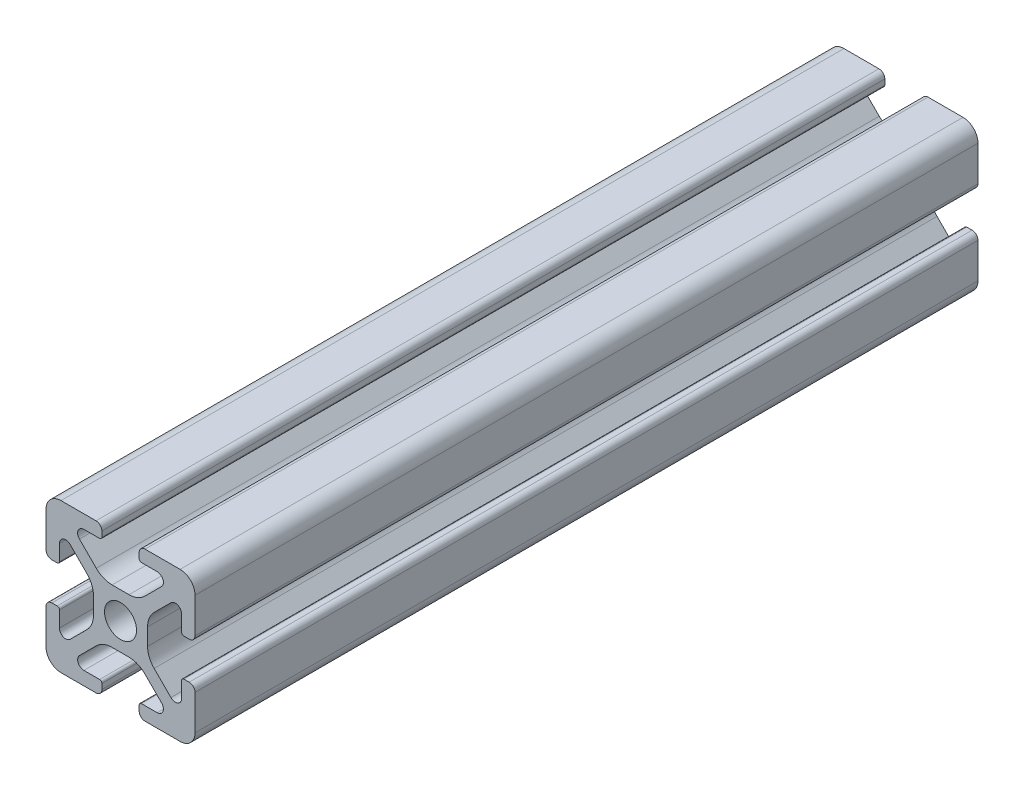
SolidWorks part; units mm, degrees
material "6061-T6 (SS)"
ref_plane "Front Plane" through (0, 0, 0) normal (0, 0, 1) x (1, 0, 0)
ref_plane "Top Plane" through (0, 0, 0) normal (0, 1, 0) x (1, 0, 0)
ref_plane "Right Plane" through (0, 0, 0) normal (1, 0, 0) x (0, 0, -1)
sketch "Sketch1" plane through (0, 0, 0) normal (0, 0, 1) x (1, 0, 0)
  line L2 (-9.9949, 7.9883) -> (-9.9949, 3.2893)
  line L3 (-7.9883, 9.9949) -> (-3.2893, 9.9949)
  line L4 (-2.5019, 9.2075) -> (-2.5019, 8.4963)
  line L5 (-2.8067, 8.1915) -> (-4.9149, 8.1915)
  line L6 (-5.5076, 6.7606) -> (-3.2528, 4.5058)
  line L7 (-6.7606, 5.5076) -> (-4.5058, 3.2528)
  line L8 (-8.1915, 4.9149) -> (-8.1915, 2.8067)
  line L9 (-8.4963, 2.5019) -> (-9.2075, 2.5019)
  line L11 (-1.1334, 3.6279) -> (1.1334, 3.6279)
  line L12 (-3.6279, 1.1334) -> (-3.6279, -1.1334)
  line L13 (8.4963, 2.5019) -> (9.2075, 2.5019)
  line L14 (8.1915, 4.9149) -> (8.1915, 2.8067)
  line L15 (9.9949, 7.9883) -> (9.9949, 3.2893)
  line L16 (7.9883, 9.9949) -> (3.2893, 9.9949)
  line L17 (2.5019, 9.2075) -> (2.5019, 8.4963)
  line L18 (2.8067, 8.1915) -> (4.9149, 8.1915)
  line L19 (3.6279, 1.1334) -> (3.6279, -1.1334)
  line L20 (5.5076, 6.7606) -> (3.2528, 4.5058)
  line L21 (6.7606, 5.5076) -> (4.5058, 3.2528)
  line L22 (-8.4963, -2.5019) -> (-9.2075, -2.5019)
  line L23 (-8.1915, -4.9149) -> (-8.1915, -2.8067)
  line L24 (-6.7606, -5.5076) -> (-4.5058, -3.2528)
  line L25 (-5.5076, -6.7606) -> (-3.2528, -4.5058)
  line L26 (-2.8067, -8.1915) -> (-4.9149, -8.1915)
  line L27 (-2.5019, -9.2075) -> (-2.5019, -8.4963)
  line L28 (-7.9883, -9.9949) -> (-3.2893, -9.9949)
  line L29 (-9.9949, -7.9883) -> (-9.9949, -3.2893)
  line L30 (9.9949, -7.9883) -> (9.9949, -3.2893)
  line L31 (7.9883, -9.9949) -> (3.2893, -9.9949)
  line L32 (2.5019, -9.2075) -> (2.5019, -8.4963)
  line L33 (2.8067, -8.1915) -> (4.9149, -8.1915)
  line L34 (5.5076, -6.7606) -> (3.2528, -4.5058)
  line L35 (6.7606, -5.5076) -> (4.5058, -3.2528)
  line L36 (8.1915, -4.9149) -> (8.1915, -2.8067)
  line L37 (8.4963, -2.5019) -> (9.2075, -2.5019)
  line L38 (-1.1334, -3.6279) -> (1.1334, -3.6279)
  circle A0 centre (0, 0) radius 2.1463
  arc A1 (-9.9949, 7.9883) -> (-7.9883, 9.9949) centre (-7.9883, 7.9883) cw
  arc A2 (-6.7606, 5.5076) -> (-8.1915, 4.9149) centre (-7.3533, 4.9149) ccw
  arc A3 (-4.9149, 8.1915) -> (-5.5076, 6.7606) centre (-4.9149, 7.3533) ccw
  arc A4 (-3.2893, 9.9949) -> (-2.5019, 9.2075) centre (-3.2893, 9.2075) cw
  arc A5 (-9.9949, 3.2893) -> (-9.2075, 2.5019) centre (-9.2075, 3.2893) ccw
  arc A6 (-8.1915, 2.8067) -> (-8.4963, 2.5019) centre (-8.4963, 2.8067) cw
  arc A7 (-2.5019, 8.4963) -> (-2.8067, 8.1915) centre (-2.8067, 8.4963) cw
  arc A8 (-1.1334, 3.6279) -> (-3.2528, 4.5058) centre (-1.1334, 6.6251) cw
  arc A9 (-3.6279, 1.1334) -> (-4.5058, 3.2528) centre (-6.6251, 1.1334) ccw
  arc A10 (8.1915, 2.8067) -> (8.4963, 2.5019) centre (8.4963, 2.8067) ccw
  arc A11 (9.9949, 3.2893) -> (9.2075, 2.5019) centre (9.2075, 3.2893) cw
  arc A12 (9.9949, 7.9883) -> (7.9883, 9.9949) centre (7.9883, 7.9883) ccw
  arc A13 (3.2893, 9.9949) -> (2.5019, 9.2075) centre (3.2893, 9.2075) ccw
  arc A14 (2.5019, 8.4963) -> (2.8067, 8.1915) centre (2.8067, 8.4963) ccw
  arc A15 (1.1334, 3.6279) -> (3.2528, 4.5058) centre (1.1334, 6.6251) ccw
  arc A16 (3.6279, 1.1334) -> (4.5058, 3.2528) centre (6.6251, 1.1334) cw
  arc A17 (6.7606, 5.5076) -> (8.1915, 4.9149) centre (7.3533, 4.9149) cw
  arc A18 (4.9149, 8.1915) -> (5.5076, 6.7606) centre (4.9149, 7.3533) cw
  arc A19 (-3.6279, -1.1334) -> (-4.5058, -3.2528) centre (-6.6251, -1.1334) cw
  arc A20 (-1.1334, -3.6279) -> (-3.2528, -4.5058) centre (-1.1334, -6.6251) ccw
  arc A21 (-2.5019, -8.4963) -> (-2.8067, -8.1915) centre (-2.8067, -8.4963) ccw
  arc A22 (-8.1915, -2.8067) -> (-8.4963, -2.5019) centre (-8.4963, -2.8067) ccw
  arc A23 (-9.9949, -3.2893) -> (-9.2075, -2.5019) centre (-9.2075, -3.2893) cw
  arc A24 (-3.2893, -9.9949) -> (-2.5019, -9.2075) centre (-3.2893, -9.2075) ccw
  arc A25 (-4.9149, -8.1915) -> (-5.5076, -6.7606) centre (-4.9149, -7.3533) cw
  arc A26 (-6.7606, -5.5076) -> (-8.1915, -4.9149) centre (-7.3533, -4.9149) cw
  arc A27 (-9.9949, -7.9883) -> (-7.9883, -9.9949) centre (-7.9883, -7.9883) ccw
  arc A28 (9.9949, -7.9883) -> (7.9883, -9.9949) centre (7.9883, -7.9883) cw
  arc A29 (6.7606, -5.5076) -> (8.1915, -4.9149) centre (7.3533, -4.9149) ccw
  arc A30 (4.9149, -8.1915) -> (5.5076, -6.7606) centre (4.9149, -7.3533) ccw
  arc A31 (3.2893, -9.9949) -> (2.5019, -9.2075) centre (3.2893, -9.2075) cw
  arc A32 (9.9949, -3.2893) -> (9.2075, -2.5019) centre (9.2075, -3.2893) ccw
  arc A33 (8.1915, -2.8067) -> (8.4963, -2.5019) centre (8.4963, -2.8067) cw
  arc A34 (2.5019, -8.4963) -> (2.8067, -8.1915) centre (2.8067, -8.4963) cw
  arc A35 (1.1334, -3.6279) -> (3.2528, -4.5058) centre (1.1334, -6.6251) cw
  arc A36 (3.6279, -1.1334) -> (4.5058, -3.2528) centre (6.6251, -1.1334) ccw
extrude "Boss-Extrude1" add sketch "Sketch1" along normal mid plane 105
